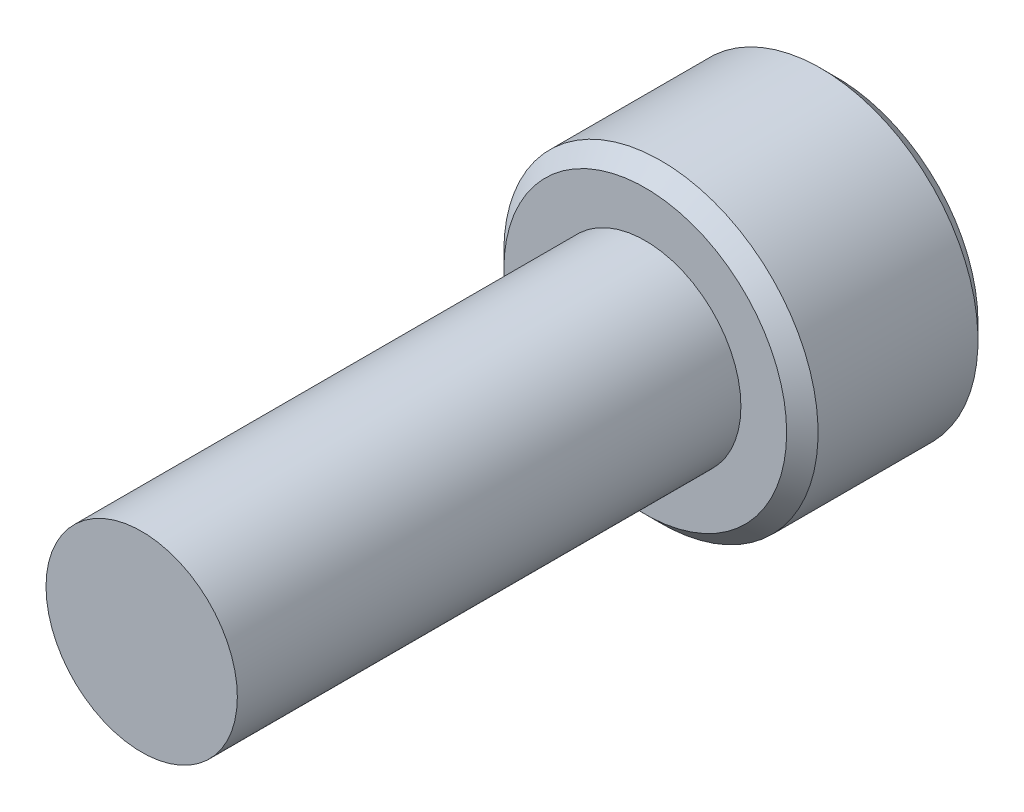
SolidWorks part; units mm, degrees
ref_plane "Front Plane" through (0, 0, 0) normal (0, 0, 1) x (1, 0, 0)
ref_plane "Top Plane" through (0, 0, 0) normal (0, 1, 0) x (1, 0, 0)
ref_plane "Right Plane" through (0, 0, 0) normal (1, 0, 0) x (0, 0, -1)
sketch "Sketch1" plane through (0, 0, 0) normal (0, 0, 1) x (1, 0, 0)
  circle A0 centre (0, 0) radius 2.413
  dimension "OD" = 4.826
extrude "Extrude1" add sketch "Sketch1" against normal blind 12.7
sketch "Sketch6" plane through (0, 0, -12.7) normal (0, 0, -1) x (-1, 0, 0)
  circle A0 centre (0, 0) radius 3.9624
  dimension "head dia" = 7.9248
extrude "Extrude2" add sketch "Sketch6" along normal blind 4.826
sketch "Sketch7" plane through (0, 0, -17.526) normal (0, 0, -1) x (-1, 0, 0)
  line L1 (0, 2.2914) -> (-1.9844, 1.1457)
  line L2 (-1.9844, 1.1457) -> (-1.9844, -1.1457)
  line L3 (-1.9844, -1.1457) -> (0, -2.2914)
  line L4 (0, -2.2914) -> (1.9844, -1.1457)
  line L5 (1.9844, -1.1457) -> (1.9844, 1.1457)
  line L6 (1.9844, 1.1457) -> (0, 2.2914)
  circle A0 centre (0, 0) radius 1.9844 construction
  dimension "hex dia" = 3.9688
extrude "Cut-Extrude1" cut sketch "Sketch7" against normal blind 2.9766
sketch "Sketch8" plane through (0, 0, -17.526) normal (0, 0, -1) x (-1, 0, 0)
  circle A0 centre (0, 0) radius 2.2914
extrude "Cut-Extrude2" cut sketch "Sketch8" against normal through all draft 45
chamfer "Chamfer1" distance 0.3962 angle 45
equation "\"D1@Cut-Extrude1\" = \"hex dia@Sketch7\"*.75"
equation "\"D1@Chamfer1\" = \"head dia@Sketch6\"*.05"
